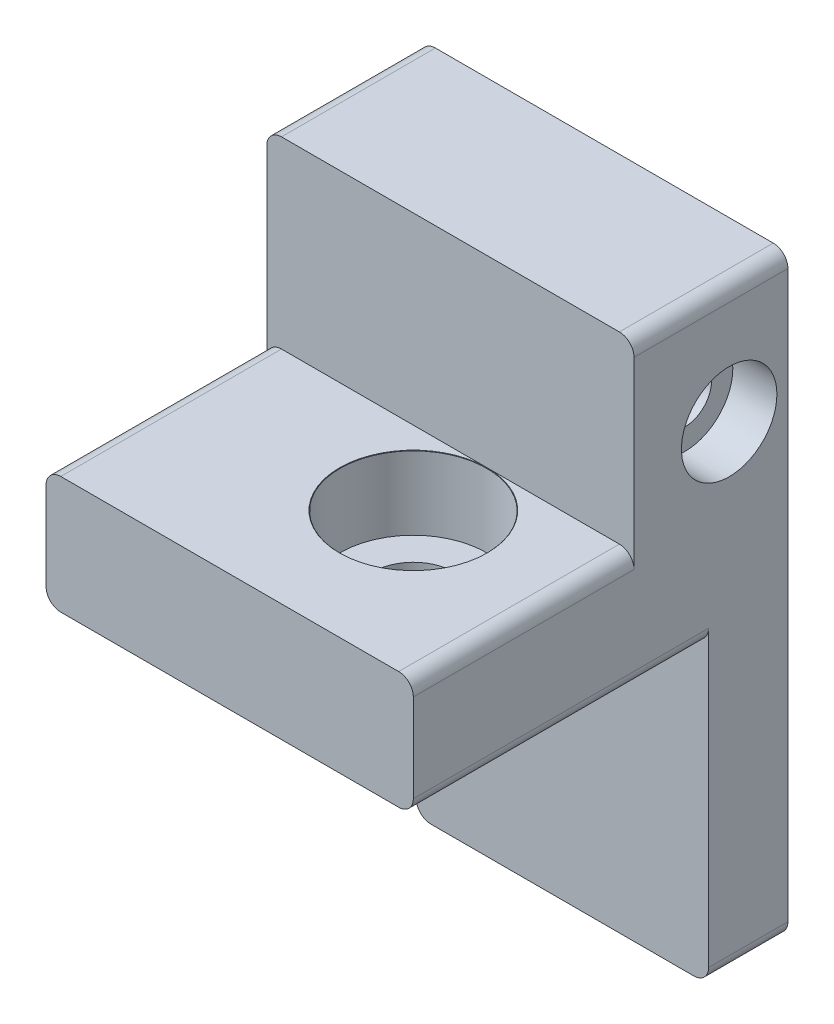
SolidWorks part; units mm, degrees
ref_plane "Front Plane" through (0, 0, 0) normal (0, 0, 1) x (1, 0, 0)
ref_plane "Top Plane" through (0, 0, 0) normal (0, 1, 0) x (1, 0, 0)
ref_plane "Right Plane" through (0, 0, 0) normal (1, 0, 0) x (0, 0, -1)
sketch "Sketch1" plane through (0, 0, 0) normal (0, 1, 0) x (1, 0, 0)
  line L0 (-10, 0) -> (-15, 0)
  line L1 (-10, -20) -> (10, -20)
  line L2 (-10, -20) -> (-10, 0)
  line L3 (-10, 20) -> (10, 20)
  line L4 (10, -20) -> (10, 20)
  line L5 (-10, -20) -> (10, 20) construction
  line L6 (-10, 20) -> (10, -20) construction
  line L7 (-15, 0) -> (-15, 20)
  line L8 (-15, 20) -> (-10, 20)
  point P0 (0, 0)
  dimension "D1" = 20
  dimension "D2" = 40
  dimension "D3" = 20
  dimension "D4" = 5
extrude "Boss-Extrude1" add sketch "Sketch1" along normal blind 8
sketch "Sketch2" plane through (0, 8, 0) normal (0, 1, 0) x (1, 0, 0)
  line L0 (0, -20) -> (0, 20) construction
  line L1 (-10, -20) -> (10, -20) construction
  line L2 (10, 20) -> (-15, 20) construction
  line L3 (-15, 10) -> (10, 10) construction
  line L4 (-15, 20) -> (-15, 0) construction
  line L5 (10, -20) -> (10, 20) construction
  point P14 (0, 10)
  point P15 (0, -10)
  dimension "D2" = 20
hole_wizard "CBORE for M5 SHCS1" positions "Sketch3" profile "Sketch4" counterbore size "M5" standard "ANSI Metric" end condition through all
sketch "Sketch3" plane through (0, 8, 0) normal (0, 1, 0) x (1, 0, 0)
  point P3 (0, 10)
  point P6 (0, -10)
sketch "Sketch4" plane through (0, 8, -10) normal (1, 0, 0) x (0, 0, 1)
  line L0 (0, 0) -> (0, 8)
  line L1 (0, 8) -> (2.75, 8)
  line L3 (2.75, 8) -> (2.75, 5)
  line L4 (5, 5) -> (2.75, 5)
  line L5 (5, 5) -> (5, 0.025)
  line L6 (5, 0.025) -> (5.025, 0)
  line L7 (5.025, 0) -> (0, 0)
  line L8 (-5, 0.025) -> (-5.025, 0) construction
  line L11 (0, -6.35) -> (0, 107.95) construction
  dimension "Thru Hole Dia." = 5.5
  dimension "Thru Hole Depth" = 8
  dimension "C'Bore Dia." = 10
  dimension "C'Bore Depth" = 5
  dimension "Near C'Sink Dia." = 10.05
  dimension "Near C'Sink Angle" = 90
sketch "Sketch5" plane through (0, 8, 0) normal (0, 1, 0) x (1, 0, 0)
  line L0 (10, -20) -> (10, 20) construction
  line L1 (-15, 18) -> (10, 18)
  line L2 (-15, 18) -> (-15, 15.025)
  line L3 (-15, 15.025) -> (10, 15.025)
  line L4 (10, 18) -> (10, 15.025)
  line L5 (10, 20) -> (-15, 20) construction
  line L6 (-15, 20) -> (-15, 0) construction
  circle A0 centre (0, 10) radius 5.025 construction
  dimension "D1" = 2
extrude "Boss-Extrude2" add sketch "Sketch5" along normal blind 12.51
sketch "Sketch6" plane through (0, 0, -18) normal (0, 0, -1) x (-1, 0, 0)
  line L0 (15, 20.51) -> (15, 8) construction
  line L1 (-10, 20.51) -> (15, 20.51)
  line L2 (-10, 20.51) -> (-10, 20)
  line L3 (-5, 17.51) -> (15, 17.51)
  line L4 (15, 20.51) -> (15, 17.51)
  line L5 (-5, 17.51) -> (-5, 8)
  line L6 (15, 8) -> (-10, 8) construction
  line L7 (-5, 8) -> (-10, 8)
  line L8 (-10, 8) -> (-10, 20)
  line L9 (15, 16.01) -> (12, 16.01)
  line L10 (12, 16.01) -> (12, 8)
  line L11 (-10, 8) -> (15, 8) construction
  line L12 (12, 8) -> (15, 8)
  line L13 (15, 8) -> (15, 16.01)
  dimension "D1" = 3
  dimension "D2" = 3
  dimension "D3" = 1.5
  dimension "D4" = 5
extrude "Boss-Extrude3" add sketch "Sketch6" along normal blind 7.5
sketch "Sketch7" plane through (0, 0, -20) normal (0, 0, -1) x (-1, 0, 0)
  line L6 (-10, 0) -> (15, 0)
  line L7 (15, 0) -> (15, 8)
  line L8 (15, 8) -> (12, 8)
  line L9 (12, 8) -> (-5, 8)
  line L10 (-5, 8) -> (-10, 8)
  line L11 (-10, 8) -> (-10, 0)
  line L12 (-10, 0) -> (15, 0)
  line L13 (15, 0) -> (15, 8)
  line L14 (15, 8) -> (12, 8)
  line L15 (12, 8) -> (-5, 8)
  line L16 (-5, 8) -> (-10, 8)
  line L17 (-10, 8) -> (-10, 0)
  dimension "D1" = 0
extrude "Boss-Extrude4" add sketch "Sketch7" along normal up to surface (5.5 mm away) up to face at (0, 15.34, -25.5)
sketch "Sketch8" plane through (0, 0, -18) normal (0, 0, -1) x (-1, 0, 0)
  line L0 (12, 16.01) -> (12, 8) construction
  line L1 (-5, 8) -> (12, 8)
  line L2 (-5, 8) -> (-5, 9.25)
  line L3 (-5, 9.25) -> (12, 9.25)
  line L4 (12, 8) -> (12, 9.25)
  dimension "D1" = 1.25
extrude "Boss-Extrude5" add sketch "Sketch8" along normal up to surface (7.5 mm away)
sketch "Sketch9" plane through (0, 0, -25.5) normal (0, 0, -1) x (-1, 0, 0)
  line L0 (-10, 0) -> (15, 0)
  line L1 (15, 0) -> (15, -5.4)
  line L2 (15, -5.4) -> (9.9, -5.4)
  line L3 (9.9, -5.4) -> (9.9, -20)
  line L4 (9.9, -20) -> (-10, -20)
  line L5 (-10, -20) -> (-10, 0)
  dimension "D1" = 5.4
  dimension "D2" = 5.1
  dimension "D3" = 20
extrude "Boss-Extrude6" add sketch "Sketch9" against normal blind 5.4
fillet "Fillet2" radius 1 10 edges at (-15, 0, -10.05) (10, 0, -0.05) (-10, 8, 10) (-15, 8, -7.5125) (10, 8, 2.4875) (-15, 20.51, -20.2625) (10, 20.51, -20.2625) (-15, -5.4, -22.8) (-9.9, -20, -22.8) (10, -20, -22.8)
sketch "Sketch10" plane through (10, 0, 0) normal (1, 0, 0) x (0, 0, -1)
  circle A0 centre (21.5, 12.48) radius 2.35 construction
  circle A1 centre (21.5, 12.48) radius 2.35
hole_wizard "CBORE for M3 SHCS1" positions "Sketch11" profile "Sketch12" counterbore size "M3" standard "ANSI Metric" end condition up to next
sketch "Sketch11" plane through (10, 0, 0) normal (1, 0, 0) x (0, 0, -1)
  point P0 (21.5, 12.48)
sketch "Sketch12" plane through (10, 12.48, -21.5) normal (0, 1, 0) x (0, 0, -1)
  line L0 (0, 0) -> (0, 5)
  line L1 (0, 5) -> (1.8, 5)
  line L3 (1.8, 5) -> (1.8, 3)
  line L4 (1.8, 3) -> (3.25, 3)
  line L5 (3.25, 3) -> (3.25, 0)
  line L7 (3.25, 0) -> (0, 0)
  line L11 (0, -6.35) -> (0, 107.95) construction
  dimension "Thru Hole Dia." = 3.6
  dimension "Thru Hole Depth" = 5
  dimension "C'Bore Dia." = 6.5
  dimension "C'Bore Depth" = 3
sketch "Sketch13" plane through (0, 0, -25.5) normal (0, 0, -1) x (-1, 0, 0)
  line L0 (-10, 7) -> (-10, 1) construction
  line L1 (-10, 7) -> (-10, 1) construction
  line L2 (-10, 4) -> (15, 4) construction
  line L3 (15, -4.4) -> (15, 16.01) construction
  line L4 (2.5, 20.51) -> (2.5, -20) construction
  line L5 (14, 20.51) -> (-9, 20.51) construction
  line L6 (-9, -20) -> (8.9, -20) construction
  circle A0 centre (10, 4) radius 2.4
  circle A1 centre (-5, 4) radius 2.4
  point P6 (10, 4)
  point P7 (-5, 4)
  point P14 (2.5, 4)
  dimension "D3" = 4.8
  dimension "D1" = 15
  dimension "D2" = 7.5
extrude "Cut-Extrude1" cut sketch "Sketch13" against normal blind 3.8
sketch "Sketch14" plane through (0, 0, -21.7) normal (0, 0, -1) x (-1, 0, 0)
  circle A0 centre (-5, 4) radius 1.65
  circle A1 centre (10, 4) radius 1.65
  dimension "D1" = 3.3
extrude "Cut-Extrude2" cut sketch "Sketch14" against normal blind 3
sketch "Sketch15" plane through (0, 8, 0) normal (0, 1, 0) x (1, 0, 0)
  line L1 (-10, 0) -> (10, 0)
  line L2 (-10, 0) -> (-10, -20)
  line L3 (-10, -20) -> (10, -20)
  line L4 (10, 0) -> (10, -20)
extrude "Cut-Extrude3" cut sketch "Sketch15" against normal through all
sketch "Sketch16" plane through (0, 0, -25.5) normal (0, 0, -1) x (-1, 0, 0)
  line L0 (12, 16.01) -> (12, 9.25) construction
  line L1 (-5, 9.25) -> (12, 9.25)
  line L2 (-5, 9.25) -> (-5, 9.05)
  line L3 (-5, 9.05) -> (12, 9.05)
  line L4 (12, 9.25) -> (12, 9.05)
  line L5 (15, -4.4) -> (15, 16.01) construction
  line L6 (12, 16.01) -> (15, 16.01)
  line L7 (12, 16.01) -> (12, 15.71)
  line L8 (12, 15.71) -> (15, 15.71)
  line L9 (15, 16.01) -> (15, 15.71)
  dimension "D1" = 0.2
  dimension "D2" = 0.3
extrude "Cut-Extrude4" cut sketch "Sketch16" against normal up to surface (7.5 mm away) up to face at (-7.3333, 14.2567, -18)
